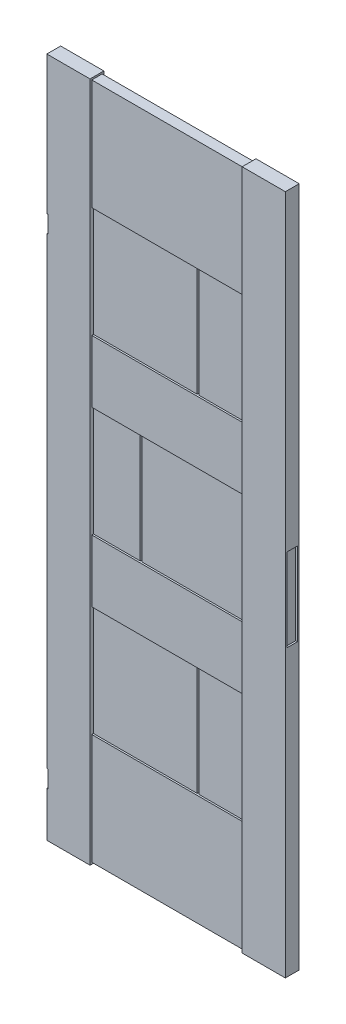
SolidWorks part; units mm, degrees
material "Mahogany"
ref_plane "Front Plane" through (0, 0, 0) normal (0, 0, 1) x (1, 0, 0)
ref_plane "Top Plane" through (0, 0, 0) normal (0, 1, 0) x (1, 0, 0)
ref_plane "Right Plane" through (0, 0, 0) normal (1, 0, 0) x (0, 0, -1)
sketch "Sketch3" plane through (0, 0, 0) normal (0, 0, 1) x (1, 0, 0)
  line L0 (0, 0) -> (0, -1970)
  line L1 (690, 0) -> (0, 0)
  line L2 (690, 0) -> (690, -1970)
  line L3 (690, -1970) -> (0, -1970)
  dimension "D1" = 690
  dimension "D2" = 1970
extrude "Boss-Extrude2" add sketch "Sketch3" against normal blind 20
sketch "Sketch4" plane through (0, 0, 0) normal (0, 0, 1) x (1, 0, 0)
  line L0 (690, 0) -> (0, 0) construction
  line L1 (125, 0) -> (565, 0)
  line L2 (125, 0) -> (125, -1970)
  line L3 (125, -1970) -> (565, -1970)
  line L4 (565, 0) -> (565, -1970)
  line L5 (0, -1970) -> (690, -1970) construction
  line L6 (0, 0) -> (0, -1970) construction
  line L7 (690, -1970) -> (690, 0) construction
  dimension "D1" = 125
  dimension "D2" = 125
extrude "Cut-Extrude1" cut sketch "Sketch4" against normal blind 5
sketch "Sketch5" plane through (0, 0, -5) normal (0, 0, 1) x (1, 0, 0)
  line L0 (565, -1970) -> (565, 0) construction
  line L1 (125, 0) -> (565, 0)
  line L2 (125, 0) -> (125, -5)
  line L3 (125, -5) -> (565, -5)
  line L4 (565, 0) -> (565, -5)
  line L5 (565, -1970) -> (565, 0) construction
  line L6 (125, -1970) -> (565, -1970)
  line L7 (125, -1970) -> (125, -1965)
  line L8 (125, -1965) -> (565, -1965)
  line L9 (565, -1970) -> (565, -1965)
  dimension "D1" = 5
  dimension "D2" = 5
extrude "Cut-Extrude2" cut sketch "Sketch5" against normal through all
sketch "Sketch6" plane through (0, 0, 0) normal (0, 0, 1) x (1, 0, 0)
  line L1 (125, -325) -> (565, -325)
  line L2 (125, -325) -> (125, -645)
  line L3 (125, -645) -> (565, -645)
  line L4 (565, -325) -> (565, -645)
  line L6 (125, 0) -> (0, 0) construction
  line L8 (125, -825) -> (565, -825)
  line L9 (125, -825) -> (125, -1145)
  line L10 (125, -1145) -> (565, -1145)
  line L11 (565, -825) -> (565, -1145)
  line L12 (125, 0) -> (125, -1970) construction
  line L13 (125, -1325) -> (565, -1325)
  line L14 (125, -1325) -> (125, -1645)
  line L15 (125, -1645) -> (565, -1645)
  line L16 (565, -1325) -> (565, -1645)
  dimension "D1" = 325
  dimension "D2" = 320
  dimension "D3" = 180
  dimension "D4" = 320
  dimension "D5" = 180
  dimension "D6" = 320
extrude "Cut-Extrude8" cut sketch "Sketch6" against normal blind 10 contours L2 L1 L4 L3 | L8 L11 L10 L9 | L13 L16 L15 L14
sketch "Sketch7" plane through (0, 0, -10) normal (0, 0, 1) x (1, 0, 0)
  line L0 (125, -325) -> (565, -325) construction
  line L1 (425, -325) -> (430, -325)
  line L2 (425, -325) -> (425, -645)
  line L3 (425, -645) -> (430, -645)
  line L4 (430, -325) -> (430, -645)
  line L5 (125, -645) -> (565, -645) construction
  line L6 (125, -325) -> (125, -645) construction
  line L7 (260, -825) -> (265, -825)
  line L8 (260, -825) -> (260, -1145)
  line L9 (260, -1145) -> (265, -1145)
  line L10 (265, -825) -> (265, -1145)
  line L11 (125, -825) -> (565, -825) construction
  line L12 (565, -1970) -> (565, 0) construction
  line L13 (425, -1325) -> (430, -1325)
  line L14 (425, -1325) -> (425, -1645)
  line L15 (425, -1645) -> (430, -1645)
  line L16 (430, -1325) -> (430, -1645)
  line L17 (125, -1325) -> (565, -1325) construction
  line L18 (125, -1325) -> (125, -1645) construction
  dimension "D1" = 300
  dimension "D2" = 5
  dimension "D3" = 5
  dimension "D4" = 300
  dimension "D5" = 5
  dimension "D6" = 300
extrude "Cut-Extrude9" cut sketch "Sketch7" against normal blind 5 contours L2 L1 L4 L3 | L7 L10 L9 L8 | L13 L16 L15 L14
mirror "Mirror1" about plane through (0, 0, -20) normal (0, 0, 1) of "Boss-Extrude2", "Cut-Extrude1", "Cut-Extrude8", "Cut-Extrude9", "Cut-Extrude2"
sketch "Sketch8" plane through (690, 0, 0) normal (1, 0, 0) x (0, 0, -1)
  line L0 (40, 0) -> (0, 0) construction
  line L1 (5, -905) -> (35, -905)
  line L2 (5, -905) -> (5, -1145)
  line L3 (5, -1145) -> (35, -1145)
  line L4 (35, -905) -> (35, -1145)
  line L5 (0, -1970) -> (0, 0) construction
  line L6 (40, -1970) -> (40, 0) construction
  dimension "D1" = 905
  dimension "D2" = 240
  dimension "D3" = 5
  dimension "D4" = 5
extrude "Cut-Extrude10" cut sketch "Sketch8" against normal blind 5
sketch "Sketch9" plane through (0, 0, 0) normal (-1, 0, 0) x (0, 0, 1)
  line L0 (-35, -400) -> (-35, -490)
  line L3 (0, -400) -> (0, -450)
  line L4 (0, -400) -> (-35, -400)
  line L5 (-35, -1790) -> (-35, -1880)
  line L8 (0, -1790) -> (0, -1840)
  line L9 (0, -1790) -> (-35, -1790)
  line L10 (0, 0) -> (0, -1970) construction
  line L11 (-5, -1880) -> (-5, -1840)
  line L12 (-5, -1840) -> (0, -1840)
  line L14 (-5, -490) -> (-5, -450)
  line L15 (-5, -450) -> (0, -450)
  line L16 (-40, 0) -> (0, 0) construction
  arc A2 (-35, -1880) -> (-5, -1880) centre (-20, -1873.75) ccw
  arc A3 (-35, -490) -> (-5, -490) centre (-20, -483.75) ccw
  dimension "D2" = 1390
  dimension "D1" = 16.25
  dimension "D8" = 83.75
  dimension "D3" = 50
  dimension "D4" = 35
  dimension "D5" = 5
  dimension "D6" = 40
  dimension "D7" = 30
  dimension "D9" = 400
extrude "Cut-Extrude11" cut sketch "Sketch9" against normal blind 3
